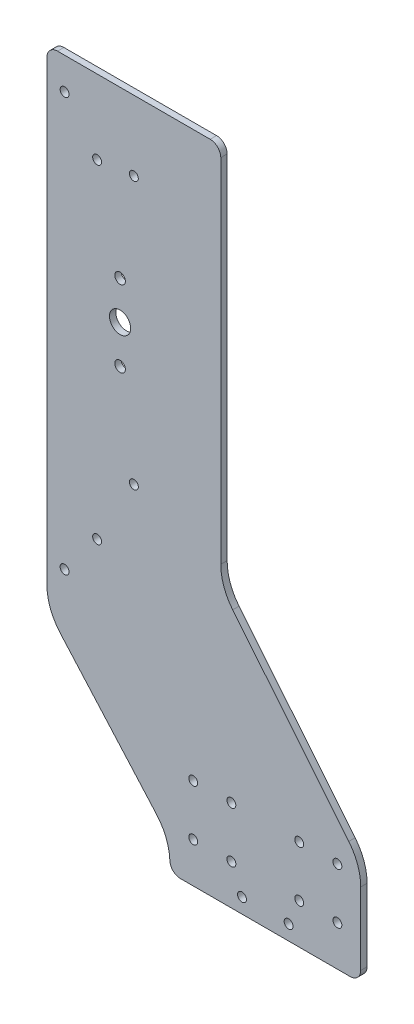
SolidWorks part; units mm, degrees
ref_plane "Front Plane" through (0, 0, 0) normal (0, 0, 1) x (1, 0, 0)
ref_plane "Top Plane" through (0, 0, 0) normal (0, 1, 0) x (1, 0, 0)
ref_plane "Right Plane" through (0, 0, 0) normal (1, 0, 0) x (0, 0, -1)
sketch "Sketch1" plane through (0, 0, 0) normal (0, 0, 1) x (1, 0, 0)
  line L0 (107, -145) -> (107, -110.8956)
  line L1 (102, -150) -> (21.9809, -150)
  line L2 (-41, 154) -> (-41, -61.5222)
  line L3 (41, 154) -> (41, -12.1044)
  line L4 (-36, 159) -> (36, 159)
  line L5 (101.3809, -95.1038) -> (46.6191, -27.8962)
  line L6 (-34.7167, -78.0958) -> (10.7167, -129.4042)
  arc A0 (102, -150) -> (107, -145) centre (102, -145) ccw
  arc A1 (107, -110.8956) -> (101.3809, -95.1038) centre (82, -110.8956) ccw
  circle A2 centre (96, -107) radius 2.1
  circle A3 centre (96, -131) radius 2.1
  circle A4 centre (78, -107) radius 2.1
  circle A5 centre (78, -131) radius 2.1
  circle A6 centre (46, -107) radius 2.1
  circle A7 centre (46, -131) radius 2.1
  circle A8 centre (28, -107) radius 2.1
  circle A9 centre (28, -131) radius 2.1
  circle A10 centre (-6.5, 81) radius 2.5
  circle A11 centre (-6.5, 45) radius 2.5
  arc A12 (-36, 159) -> (-41, 154) centre (-36, 154) ccw
  arc A13 (-41, -61.5222) -> (-34.7167, -78.0958) centre (-16, -61.5222) ccw
  arc A14 (41, 154) -> (36, 159) centre (36, 154) ccw
  arc A15 (41, -12.1044) -> (46.6191, -27.8962) centre (66, -12.1044) ccw
  arc A16 (16.9809, -145) -> (10.7167, -129.4042) centre (-8, -145.9778) ccw
  circle A17 centre (-6.5, 63) radius 5
  circle A18 centre (51, -143) radius 2.1
  circle A19 centre (73, -143) radius 2.1
  arc A20 (16.9809, -145) -> (21.9809, -150) centre (21.9809, -145) ccw
  circle A21 centre (0, 126) radius 2.1
  circle A22 centre (0, 0) radius 2.1
  circle A23 centre (-32.6667, 144) radius 2.1
  circle A24 centre (-17.3333, 124) radius 2.1
  circle A25 centre (-17.3333, -31) radius 2.1
  circle A26 centre (-32.6667, -51) radius 2.1
extrude "Boss-Extrude1" add sketch "Sketch1" along normal mid plane 3
